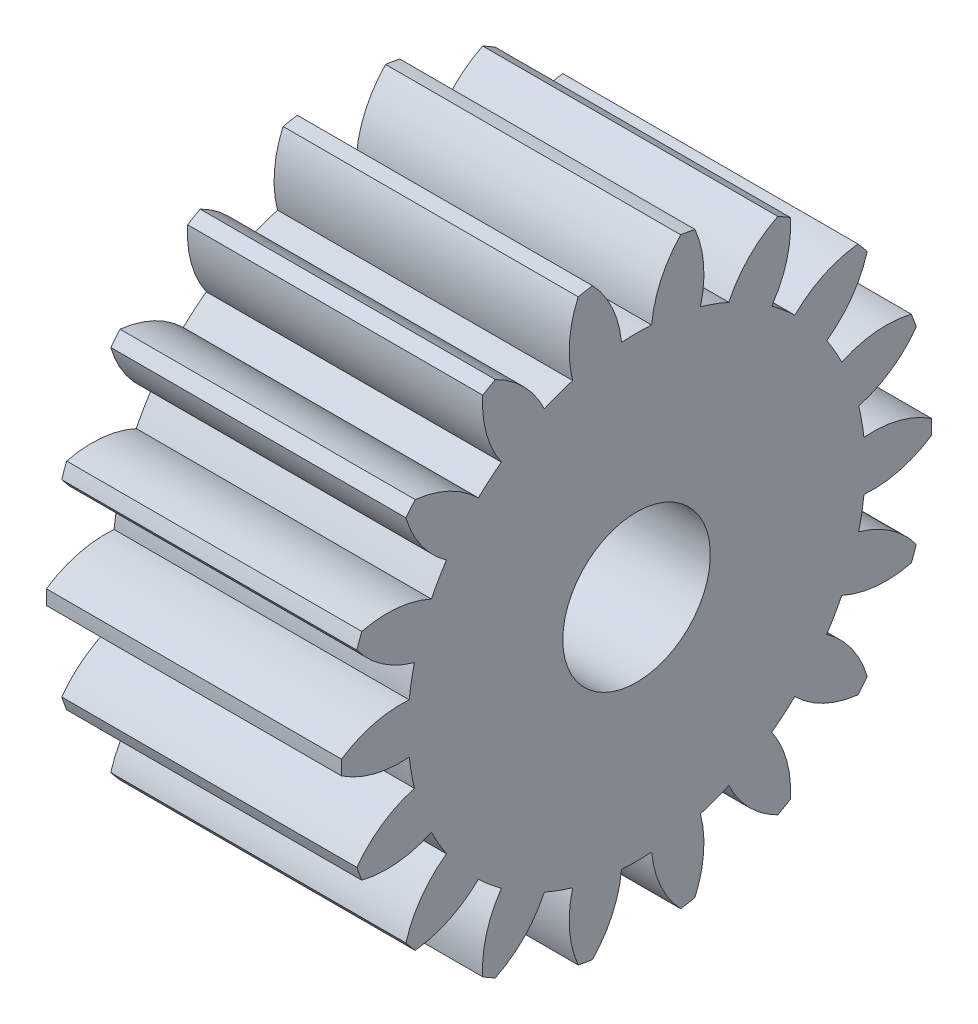
SolidWorks part; units mm, degrees
ref_plane "Plane1" through (0, 0, 0) normal (0, 0, 1) x (1, 0, 0)
ref_plane "Plane2" through (0, 0, 0) normal (0, 1, 0) x (1, 0, 0)
ref_plane "Plane3" through (0, 0, 0) normal (1, 0, 0) x (0, 0, -1)
other "Configuration Table"
sketch "HoldingSke" plane through (0, 0, 0) normal (0, 1, 0) x (1, 0, 0)
  line L0 (0, 0) -> (0.9511, -0.309)
  line L1 (-15, 0) -> (100, 0) construction
  line L2 (0, 0) -> (-2.1039, 2.3779)
  line L3 (0, 0) -> (-11.863, 4.5341)
  line L4 (0, 0) -> (8.2133, 2.6687)
  line L5 (0, 0) -> (-46.8476, -17.4728)
  line L6 (0, 0) -> (-8.2896, -5.593)
  line L7 (-2.1039, 2.3779) -> (8.6586, 51.2059)
  line L8 (-76.2, 54.61) -> (-75.3, 54.61)
  line L9 (-71.009, 38.7566) -> (-53.1078, 45.2721)
  line L10 (-76.2, 71.12) -> (104.1128, 71.12)
  line L11 (0, 0) -> (-10, 0)
  line L12 (-76.2, 101.6) -> (-76.162, 101.6)
  line L13 (24.9733, 27.94) -> (52.9518, 28.4284)
  line L14 (24.9733, 27.94) -> (24.9743, 27.94)
  line L15 (24.9733, 27.94) -> (100.4006, 29.5858)
  line L16 (-63.627, -1) -> (-12.827, -1)
  circle A0 centre (0, 0) radius 2.5
  circle A1 centre (0, 0) radius 7.749
  circle A2 centre (0, 0) radius 37.5
  circle A3 centre (0, 0) radius 2.5
  dimension "MHD" = 15.498
  dimension "Hub_dia" = 75
  dimension "Bore" = 5
  dimension "MBD" = 5
  dimension "Num_teeth" = 18
  dimension "Pitch" = 1
  dimension "Overall_len" = 50
  dimension "Show_teeth" = 18
  dimension "Thickness" = 10
  dimension "OAL" = 50.0001
  dimension "T_dim" = 0.9
  dimension "Ap" = 20
  dimension "H" = 19.05
  dimension "Pitch_radius" = 180.3128
  dimension "Width" = 10
  dimension "Backlash" = 0.038
  dimension "Addendum_fac" = 1
  dimension "Dedendum_fac" = 1.25
  dimension "Clearance_fac" = 0.25
  dimension "Dedendum_add" = 0.001
  dimension "Module" = 1
sketch "BasProSke" plane through (0, 0, 0) normal (0, 1, 0) x (1, 0, 0)
  line L0 (-10, 0) -> (60, 0) construction
  line L1 (0, 0) -> (0, 10)
  line L2 (0, 0) -> (10, 0)
  line L3 (10, 0) -> (10, 10)
  line L4 (10, 10) -> (0, 10)
  dimension "Thickness" = 10
  dimension "Diameter" = 20
revolve "Base-Revolve" add sketch "BasProSke" angle 360 about L0
sketch "TooCutSke" plane through (0, 0, 0) normal (1, 0, 0) x (0, 0, -1)
  line L1 (0, 0) -> (0, 107) construction
  line L2 (0, 0) -> (-0.8509, 8.9597) construction
  line L3 (0, 0) -> (-3.1157, 17.6701) construction
  line L4 (-0.8509, 8.9597) -> (-1.5579, 8.835) construction
  arc A0 (0.5106, 7.7322) -> (-0.5106, 7.7322) centre (0, 0) ccw
  arc A1 (1.5152, 9.9102) -> (-1.5152, 9.9102) centre (0, 0) ccw
  circle A2 centre (0, 0) radius 9 construction
  circle A3 centre (0, 0) radius 8.4572 construction
  arc A4 (-0.5106, 7.7322) -> (-1.5152, 9.9102) centre (-4.0952, 7.3996) ccw
  arc A5 (1.5152, 9.9102) -> (0.5106, 7.7322) centre (4.0952, 7.3996) ccw
  dimension "Root_dia" = 15.498
  dimension "Overcut_dia" = 20.0508
  dimension "Pitch_dia" = 18
  dimension "Base_dia" = 16.9145
  dimension "Flank_rad" = 3.6
  dimension "Half_ang" = 10
  dimension "Half_CT" = 0.7179
extrude "ToothCut" cut sketch "TooCutSke" along normal through all
fillet "Breaks" [suppressed] radius 0.02
fillet "RootFillets" [suppressed] radius 0.251
pattern_circular "TeethCuts" count 18 every 20 about axis through (-10, 0, 0) along (1, 0, 0) of "ToothCut", "RootFillets", "Breaks"
sketch "HubNeaOneSke" plane through (0, 0, 0) normal (-1, 0, 0) x (0, 0, 1)
  circle A0 centre (0, 0) radius 7.749
  dimension "Diameter" = 15.498
extrude "HubNearOne" [suppressed] add sketch "HubNeaOneSke" along normal blind 40.0001
sketch "HubNeaBotSke" plane through (0, 0, 0) normal (-1, 0, 0) x (0, 0, 1)
  circle A0 centre (0, 0) radius 7.749
  dimension "Diameter" = 15.498
extrude "HubNearBoth" [suppressed] add sketch "HubNeaBotSke" along normal blind 20
ref_plane "FarPln" through (10, 0, 0) normal (1, 0, 0) x (0, 0, -1)
sketch "HubFarSke" plane through (10, 0, 0) normal (1, 0, 0) x (0, 0, -1)
  circle A0 centre (0, 0) radius 7.749
  dimension "Diameter" = 15.498
extrude "HubFar" [suppressed] add sketch "HubFarSke" along normal blind 20
sketch "BorSke" plane through (0, 0, 0) normal (1, 0, 0) x (0, 0, -1)
  circle A0 centre (0, 0) radius 2.5
  dimension "Diameter" = 5
extrude "Bore" cut sketch "BorSke" along normal mid plane 100.0001
sketch "KeySke" plane through (0, 0, 0) normal (1, 0, 0) x (0, 0, -1)
  line L0 (-1, 0) -> (-1, 3.4)
  line L1 (-1, 3.4) -> (1, 3.4)
  line L2 (1, 3.4) -> (1, 0)
  line L3 (0, 0) -> (0, 34) construction
  line L4 (-1, 0) -> (1, 0)
  dimension "Offset" = 3.4
  dimension "Width" = 2
extrude "Keyway" [suppressed] cut sketch "KeySke" along normal mid plane 100.0001
pattern_circular "Keyway2" [suppressed] count 2 every 90 about axis through (-10, 0, 0) along (1, 0, 0)
equation "' \"Module@HoldingSke\" = 6.35"
equation "' \"Num_teeth@HoldingSke\" = 12"
equation "' \"Ap@HoldingSke\" =  20"
equation "' \"Ap@HoldingSke\" = 20"
equation "' \"Width@HoldingSke\" = 0.5 * 25.4"
equation "' \"Hub_dia@HoldingSke\"= 1 * 25.4"
equation "' \"Hub_dia@HoldingSke\" = 1 * 25.4"
equation "' \"Overall_len@HoldingSke\" = 1.0 * 25.4"
equation "' \"Bore@HoldingSke\" = 0.75 * 25.4"
equation "' \"T_dim@HoldingSke\" = 0.1 * 25.4"
equation "' \"Width@KeySke\" = 0.25 * 25.4"
equation "' \"Show_teeth@HoldingSke\" = 13"
equation "' \"Backlash@HoldingSke\" = 0.009 * 25.4"
equation "' \"Addendum_fac@HoldingSke\" = 1.0"
equation "' \"Dedendum_fac@HoldingSke\" = 1.25"
equation "' \"Dedendum_add@HoldingSke\" = 0.00005 * 25.4"
equation "' \"Clearance_fac@HoldingSke\" = 0.25"
equation "\"Pitch@HoldingSke\" = 1 / \"Module@HoldingSke\""
equation "\"Overcut_dia@TooCutSke\" = (\"Num_teeth@HoldingSke\" + 2 * \"Addendum_fac@HoldingSke\") / \"Pitch@HoldingSke\" + 0.002 * 25.4"
equation "\"Pitch_dia@TooCutSke\" = \"Num_teeth@HoldingSke\" / \"Pitch@HoldingSke\""
equation "\"Base_dia@TooCutSke\" = \"Num_teeth@HoldingSke\" / \"Pitch@HoldingSke\" * cos((\"Ap@HoldingSke\"  * 3.14159265 / 180))"
equation "\"Root_dia@TooCutSke\" = (\"Num_teeth@HoldingSke\" + 2) / \"Pitch@HoldingSke\" - 2 * (\"Addendum_fac@HoldingSke\" + \"Dedendum_fac@HoldingSke\") / \"Pitch@HoldingSke\" - \"Dedendum_add@HoldingSke\" * 2"
equation "\"Half_ang@TooCutSke\" = 180 / \"Num_teeth@HoldingSke\""
equation "\"Half_CT@TooCutSke\" = \"Num_teeth@HoldingSke\" / \"Pitch@HoldingSke\" * sin((3.14159265 / 2 / \"Num_teeth@HoldingSke\")) / 2 - 7 * \"Backlash@HoldingSke\" / 4"
equation "\"Flank_rad@TooCutSke\" = \"Num_teeth@HoldingSke\" / \"Pitch@HoldingSke\" / 5"
equation "\"Radius@RootFillets\" = \"Clearance_fac@HoldingSke\" / \"Pitch@HoldingSke\" + \"Dedendum_add@HoldingSke\""
equation "\"Break_rad@Breaks\" = 0.02 / \"Pitch@HoldingSke\""
equation "\"Thickness@HoldingSke\" = \"Width@HoldingSke\""
equation "\"OAL@HoldingSke\" = \"Thickness@HoldingSke\""
equation "\"MHD@HoldingSke\" = (\"Num_teeth@HoldingSke\" + 2) / \"Pitch@HoldingSke\" - 2 * (\"Addendum_fac@HoldingSke\" + \"Dedendum_fac@HoldingSke\")  / \"Pitch@HoldingSke\" - \"Dedendum_add@HoldingSke\" * 2"
equation "\"MBD@HoldingSke\" = (\"Num_teeth@HoldingSke\" + 2) / \"Pitch@HoldingSke\" - 2 * (\"Addendum_fac@HoldingSke\" + \"Dedendum_fac@HoldingSke\")  / \"Pitch@HoldingSke\" - \"Dedendum_add@HoldingSke\" * 2 - 0.002 * 25.4"
equation "\"MHD@HoldingSke\" = ((sgn( \"MHD@HoldingSke\" - \"Hub_dia@HoldingSke\" )-1)*( \"MHD@HoldingSke\" - \"Hub_dia@HoldingSke\" ))/-2+ \"Hub_dia@HoldingSke\""
equation "\"MBD@HoldingSke\" = ((sgn( \"MBD@HoldingSke\" - \"Bore@HoldingSke\" )-1)*( \"MBD@HoldingSke\" - \"Bore@HoldingSke\" ))/-2+ \"Bore@HoldingSke\""
equation "\"OAL@HoldingSke\" = ((sgn( \"OAL@HoldingSke\" - \"Overall_len@HoldingSke\" )+1)*( \"OAL@HoldingSke\" - \"Overall_len@HoldingSke\" ))/2 + \"Overall_len@HoldingSke\" + 0.000002 * 25.4"
equation "\"Num_teeth@TeethCuts\" = int( \"Show_teeth@HoldingSke\" ) + 1"
equation "\"Num_teeth@TeethCuts\" = ((sgn( \"Num_teeth@TeethCuts\" - \"Num_teeth@HoldingSke\" )-1)*( \"Num_teeth@TeethCuts\" - \"Num_teeth@HoldingSke\" ))/-2+ \"Num_teeth@HoldingSke\""
equation "\"Num_teeth@TeethCuts\" = ((sgn( \"Num_teeth@TeethCuts\" - 2.0)+1)*( \"Num_teeth@TeethCuts\" - 2.0))/2 +2.0"
equation "\"Angle@TeethCuts\" = 360.0 / \"Num_teeth@HoldingSke\""
equation "\"Diameter@BasProSke\" = (\"Num_teeth@HoldingSke\" + 2 * \"Addendum_fac@HoldingSke\") / \"Pitch@HoldingSke\""
equation "\"Thickness@BasProSke\"  = \"Thickness@HoldingSke\""
equation "' \"Fillet_rad@BasProSke\" =  \"Thickness@HoldingSke\" * 0.05"
equation "' \"Fillet_rad@BasProSke\" = \"Thickness@HoldingSke\" * 0.05"
equation "\"MHD@HoldingSke\" = ((sgn( \"MHD@HoldingSke\" - \"Root_dia@TooCutSke\" )-1)*( \"MHD@HoldingSke\" - \"Root_dia@TooCutSke\" ))/-2+ \"Root_dia@TooCutSke\""
equation "\"Diameter@HubNeaOneSke\" = \"MHD@HoldingSke\""
equation "\"Length@HubNearOne\" = \"OAL@HoldingSke\" - \"Thickness@BasProSke\""
equation "\"Diameter@HubNeaBotSke\" = \"MHD@HoldingSke\""
equation "\"Length@HubNearBoth\" = ( \"OAL@HoldingSke\" - \"Thickness@BasProSke\" ) / 2.0"
equation "\"Thickness@FarPln\" = \"Thickness@BasProSke\""
equation "\"Diameter@HubFarSke\" = \"MHD@HoldingSke\""
equation "\"Length@HubFar\" = ( \"OAL@HoldingSke\" - \"Thickness@BasProSke\" ) / 2.0"
equation "\"Diameter@BorSke\" = \"MBD@HoldingSke\""
equation "\"D1@Bore\" = \"OAL@HoldingSke\" * 2.0"
equation "\"D1@Keyway\" = \"OAL@HoldingSke\" * 2.0"
equation "\"Offset@KeySke\" = \"T_dim@HoldingSke\" + \"MBD@HoldingSke\" / 2.0"
